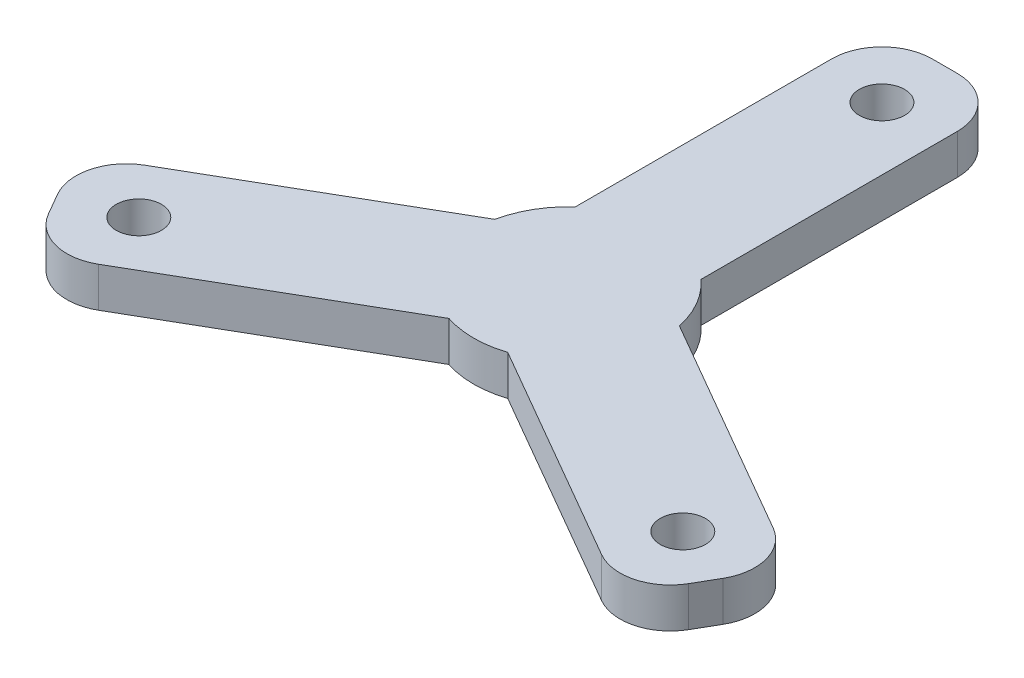
SolidWorks part; units mm, degrees
ref_plane "Front Plane" through (0, 0, 0) normal (0, 0, 1) x (1, 0, 0)
ref_plane "Top Plane" through (0, 0, 0) normal (0, 1, 0) x (1, 0, 0)
ref_plane "Right Plane" through (0, 0, 0) normal (1, 0, 0) x (0, 0, -1)
sketch "Sketch1" plane through (0, 0, 0) normal (0, 1, 0) x (1, 0, 0)
  line L0 (2.5, 4.3301) -> (-2.5, -4.3301)
  line L1 (-5, 0) -> (5, 0)
  line L2 (-5, 0) -> (-5, 26)
  line L3 (-1, 30) -> (1, 30)
  line L4 (5, 0) -> (5, 26)
  line L5 (-2.5, -4.3301) -> (20.0167, -17.3301)
  line L6 (2.5, 4.3301) -> (25.0167, -8.6699)
  line L7 (26.4808, -14.134) -> (25.4808, -15.866)
  line L8 (2.5, -4.3301) -> (-2.5, 4.3301)
  line L9 (-2.5, 4.3301) -> (-25.0167, -8.6699)
  line L10 (2.5, -4.3301) -> (-20.0167, -17.3301)
  line L11 (-25.4808, -15.866) -> (-26.4808, -14.134)
  circle A2 centre (0, 25) radius 1.8
  circle A3 centre (21.6506, -12.5) radius 1.8
  circle A4 centre (-21.6506, -12.5) radius 1.8
  circle A5 centre (0, 0) radius 5
  arc A6 (-5, 26) -> (-1, 30) centre (-1, 26) cw
  arc A7 (1, 30) -> (5, 26) centre (1, 26) cw
  arc A8 (25.0167, -8.6699) -> (26.4808, -14.134) centre (23.0167, -12.134) cw
  arc A9 (25.4808, -15.866) -> (20.0167, -17.3301) centre (22.0167, -13.866) cw
  arc A10 (-20.0167, -17.3301) -> (-25.4808, -15.866) centre (-22.0167, -13.866) cw
  arc A11 (-26.4808, -14.134) -> (-25.0167, -8.6699) centre (-23.0167, -12.134) cw
  circle A12 centre (0, 0) radius 7.5
  point P12 (0, 0)
  point P18 (-5, 30)
  point P37 (0, 0)
  dimension "D1" = 25
  dimension "D2" = 10
  dimension "D3" = 3.6
  dimension "D6" = 4
  dimension "D7" = 4
  dimension "D9" = 15
  dimension "D4" = 30
  dimension "D5" = 3
  dimension "D8" = 3
extrude "Boss-Extrude1" add sketch "Sketch1" along normal blind 3.175 contours L1 A5 L0 | A7 L3 A6 L2 L9 A5 L6 L4 A2 | A9 L7 A8 L6 L4 A5 L10 L5 A3 | A11 L11 A10 L10 L5 A5 L2 L9 A4 | A5 L9 L2 | A5 L4 L6 | L8 A5 L1 | L0 A5 L8 | L1 A5 L0 | L8 A5 L1 | L0 A5 L8 | A5 L5 L10 | L6 A12 L4 | L5 A12 L6 L4 A5 L10 | L10 A12 L5 | L9 A12 L10 L5 A5 L2 | L2 A12 L9 | L4 A12 L2 L9 A5 L6
sketch "Sketch2" plane through (0, 3.175, 0) normal (0, 1, 0) x (1, 0, 0)
  circle A0 centre (0, 0) radius 0.5
  dimension "D1" = 1
